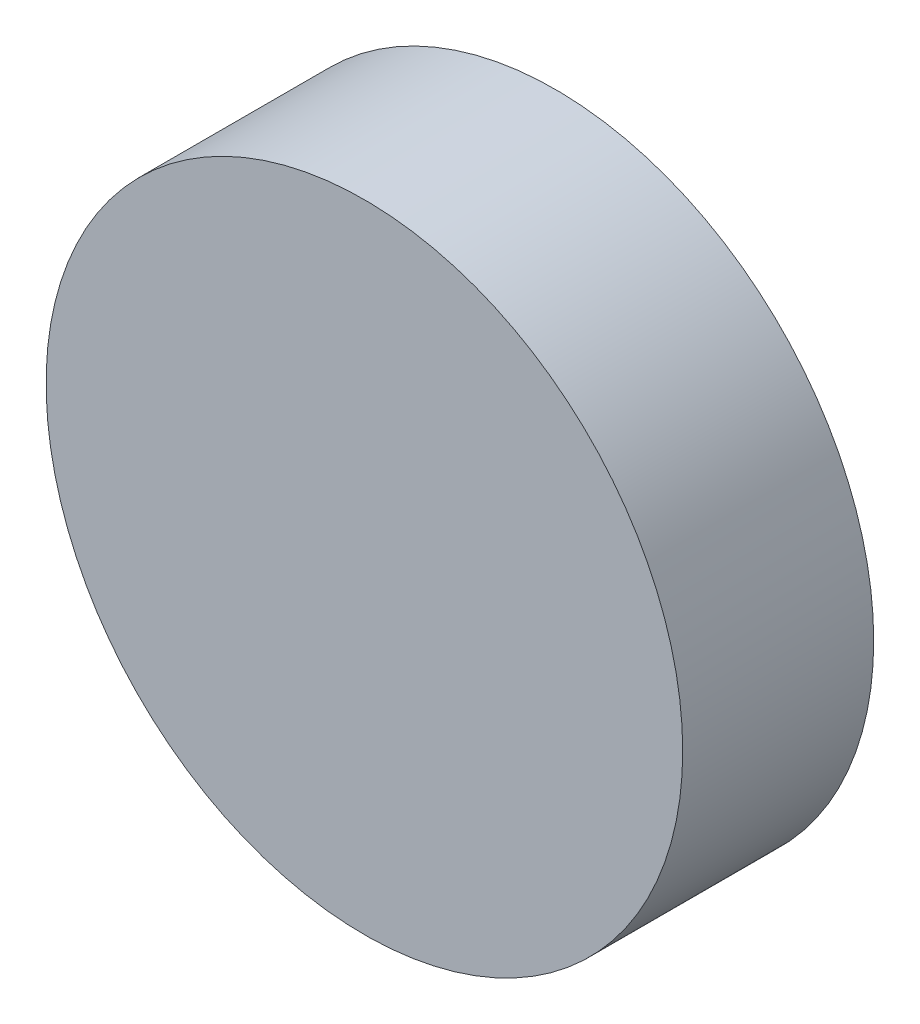
SolidWorks part; units mm, degrees
ref_plane "Front Plane" through (0, 0, 0) normal (0, 0, 1) x (1, 0, 0)
ref_plane "Top Plane" through (0, 0, 0) normal (0, 1, 0) x (1, 0, 0)
ref_plane "Right Plane" through (0, 0, 0) normal (1, 0, 0) x (0, 0, -1)
sketch "Sketch1" plane through (0, 0, 0) normal (0, 0, 1) x (1, 0, 0)
  circle A0 centre (0, 0) radius 10
  dimension "D1" = 20
extrude "Boss-Extrude1" add sketch "Sketch1" along normal blind 6
